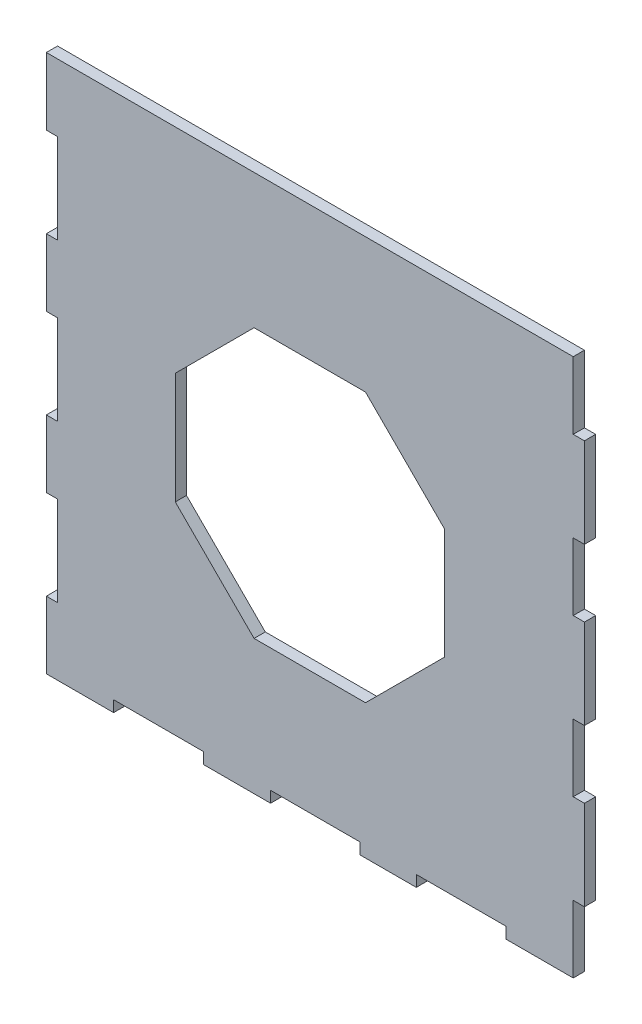
SolidWorks part; units mm, degrees
ref_plane "Front Plane" through (0, 0, 0) normal (0, 0, 1) x (1, 0, 0)
ref_plane "Top Plane" through (0, 0, 0) normal (0, 1, 0) x (1, 0, 0)
ref_plane "Right Plane" through (0, 0, 0) normal (1, 0, 0) x (0, 0, -1)
sketch "Sketch1" plane through (0, 0, 0) normal (0, 0, 1) x (1, 0, 0)
  line L1 (74.6125, -76.2) -> (-74.6125, -76.2)
  line L2 (74.6125, -76.2) -> (74.6125, 76.2)
  line L3 (74.6125, 76.2) -> (-74.6125, 76.2)
  line L4 (-74.6125, -76.2) -> (-74.6125, 76.2)
  line L5 (74.6125, -76.2) -> (-74.6125, 76.2) construction
  line L6 (74.6125, 76.2) -> (-74.6125, -76.2) construction
  line L7 (-74.6125, 57.15) -> (-71.4375, 57.15)
  line L8 (-74.6125, 57.15) -> (-74.6125, 31.75)
  line L9 (-74.6125, 31.75) -> (-71.4375, 31.75)
  line L10 (-71.4375, 57.15) -> (-71.4375, 31.75)
  line L11 (-74.6125, -31.75) -> (-71.4375, -31.75)
  line L12 (-74.6125, -31.75) -> (-74.6125, -57.15)
  line L13 (-74.6125, -57.15) -> (-71.4375, -57.15)
  line L14 (-71.4375, -31.75) -> (-71.4375, -57.15)
  line L15 (-74.6125, 12.7) -> (-71.4375, 12.7)
  line L16 (-74.6125, 12.7) -> (-74.6125, -12.7)
  line L17 (-74.6125, -12.7) -> (-71.4375, -12.7)
  line L18 (-71.4375, 12.7) -> (-71.4375, -12.7)
  line L19 (74.6125, 57.15) -> (77.7875, 57.15)
  line L20 (74.6125, 57.15) -> (74.6125, 31.75)
  line L21 (74.6125, 31.75) -> (77.7875, 31.75)
  line L22 (77.7875, 57.15) -> (77.7875, 31.75)
  line L23 (74.6125, 12.7) -> (77.7875, 12.7)
  line L24 (74.6125, 12.7) -> (74.6125, -12.7)
  line L25 (74.6125, -12.7) -> (77.7875, -12.7)
  line L26 (77.7875, 12.7) -> (77.7875, -12.7)
  line L27 (74.6125, -31.75) -> (77.7875, -31.75)
  line L28 (74.6125, -31.75) -> (74.6125, -57.15)
  line L29 (74.6125, -57.15) -> (77.7875, -57.15)
  line L30 (77.7875, -31.75) -> (77.7875, -57.15)
  line L31 (-55.5625, -76.2) -> (-30.1625, -76.2)
  line L32 (-55.5625, -76.2) -> (-55.5625, -73.025)
  line L33 (-55.5625, -73.025) -> (-30.1625, -73.025)
  line L34 (-30.1625, -76.2) -> (-30.1625, -73.025)
  line L35 (-11.1125, -76.2) -> (14.2875, -76.2)
  line L36 (-11.1125, -76.2) -> (-11.1125, -73.025)
  line L37 (-11.1125, -73.025) -> (14.2875, -73.025)
  line L38 (14.2875, -76.2) -> (14.2875, -73.025)
  line L39 (30.1625, -76.2) -> (55.5625, -76.2)
  line L40 (30.1625, -76.2) -> (30.1625, -73.025)
  line L41 (30.1625, -73.025) -> (55.5625, -73.025)
  line L42 (55.5625, -76.2) -> (55.5625, -73.025)
  point P0 (0, 0)
  dimension "D1" = 149.225
  dimension "D2" = 152.4
  dimension "D3" = 3.175
  dimension "D4" = 3.175
  dimension "D5" = 3.175
  dimension "D6" = 25.4
  dimension "D7" = 25.4
  dimension "D8" = 25.4
  dimension "D9" = 25.4
  dimension "D10" = 25.4
  dimension "D11" = 25.4
  dimension "D12" = 3.175
  dimension "D13" = 3.175
  dimension "D14" = 3.175
  dimension "D15" = 19.05
  dimension "D16" = 19.05
  dimension "D17" = 19.05
  dimension "D18" = 19.05
  dimension "D19" = 19.05
  dimension "D20" = 19.05
  dimension "D21" = 3.175
  dimension "D22" = 3.175
  dimension "D23" = 3.175
  dimension "D24" = 25.4
  dimension "D25" = 25.4
  dimension "D26" = 25.4
  dimension "D27" = 19.05
  dimension "D28" = 19.05
  dimension "D29" = 19.05
extrude "Boss-Extrude1" add sketch "Sketch1" along normal blind 3.175 contours L42 L1 L2 L3 L4 L7 L10 L9 L15 L18 L17 L11 L14 L13 L32 L33 L34 L36 L37 L38 L40 L41 | L22 L21 L20 L19 | L26 L25 L24 L23 | L30 L29 L28 L27
sketch "Sketch2" plane through (0, 0, 3.175) normal (0, 0, 1) x (1, 0, 0)
  line L0 (74.6125, 76.2) -> (-74.6125, 76.2) construction
  line L1 (-15.7815, 38.1) -> (-38.1, 15.7815)
  line L2 (-38.1, 15.7815) -> (-38.1, -15.7815)
  line L3 (-38.1, -15.7815) -> (-15.7815, -38.1)
  line L4 (-15.7815, -38.1) -> (15.7815, -38.1)
  line L5 (15.7815, -38.1) -> (38.1, -15.7815)
  line L6 (38.1, -15.7815) -> (38.1, 15.7815)
  line L7 (38.1, 15.7815) -> (15.7815, 38.1)
  line L8 (15.7815, 38.1) -> (-15.7815, 38.1)
  circle A0 centre (0, 0) radius 38.1 construction
  dimension "D1" = 38.1
extrude "Cut-Extrude1" cut sketch "Sketch2" against normal through all
